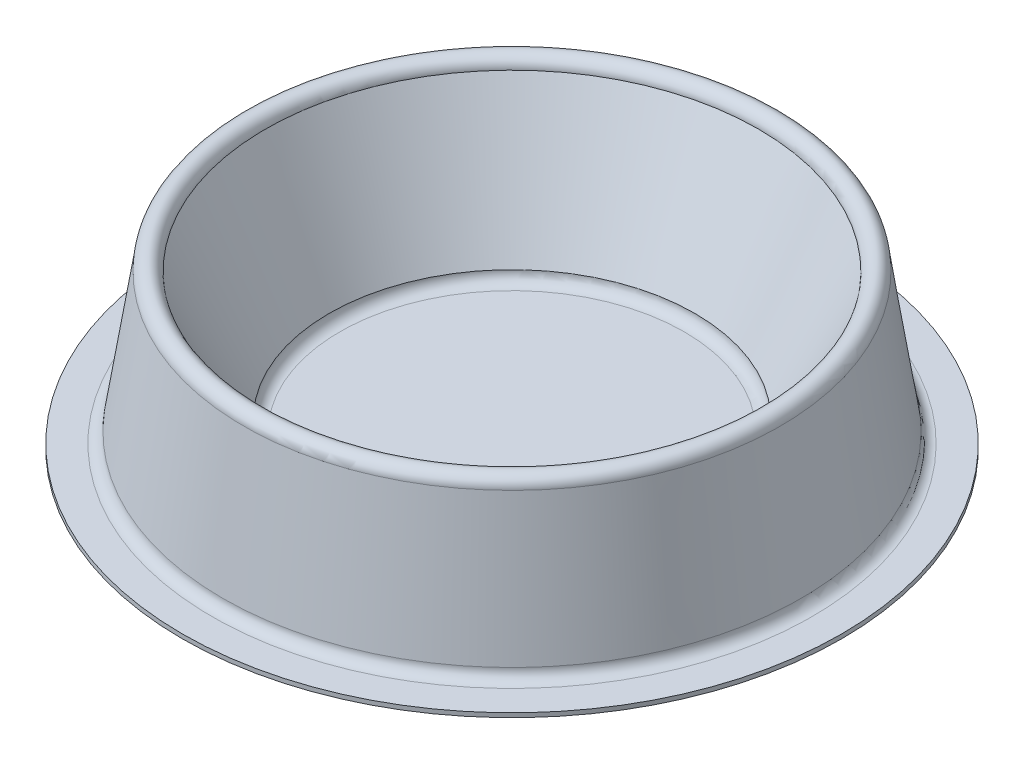
SolidWorks part; units mm, degrees
ref_plane "Front Plane" through (0, 0, 0) normal (0, 0, 1) x (1, 0, 0)
ref_plane "Top Plane" through (0, 0, 0) normal (0, 1, 0) x (1, 0, 0)
ref_plane "Right Plane" through (0, 0, 0) normal (1, 0, 0) x (0, 0, -1)
sketch "Sketch1" plane through (0, 0, 0) normal (0, 0, 1) x (1, 0, 0)
  line L0 (-27.3189, 0) -> (-20.3189, 0)
  line L1 (-17.8189, 2.5) -> (-12.8189, 35)
  line L2 (50.1811, 2.5) -> (50.1811, 57.0298) construction
  line L3 (-7.8189, 35) -> (7.1811, 5)
  line L4 (9.6811, 2.5) -> (50.1811, 2.5)
  arc A0 (-20.3189, 0) -> (-17.8189, 2.5) centre (-20.3189, 2.5) ccw
  arc A1 (-7.8189, 35) -> (-12.8189, 35) centre (-10.3189, 35) ccw
  arc A2 (7.1811, 5) -> (9.6811, 2.5) centre (9.6811, 5) ccw
  dimension "D2" = 5
  dimension "D3" = 5
  dimension "D4" = 5
  dimension "D6" = 35
  dimension "D1" = 7
  dimension "D5" = 10
  dimension "D7" = 20
revolve "Revolve-Thin1" add sketch "Sketch1" angle 360 about L2
